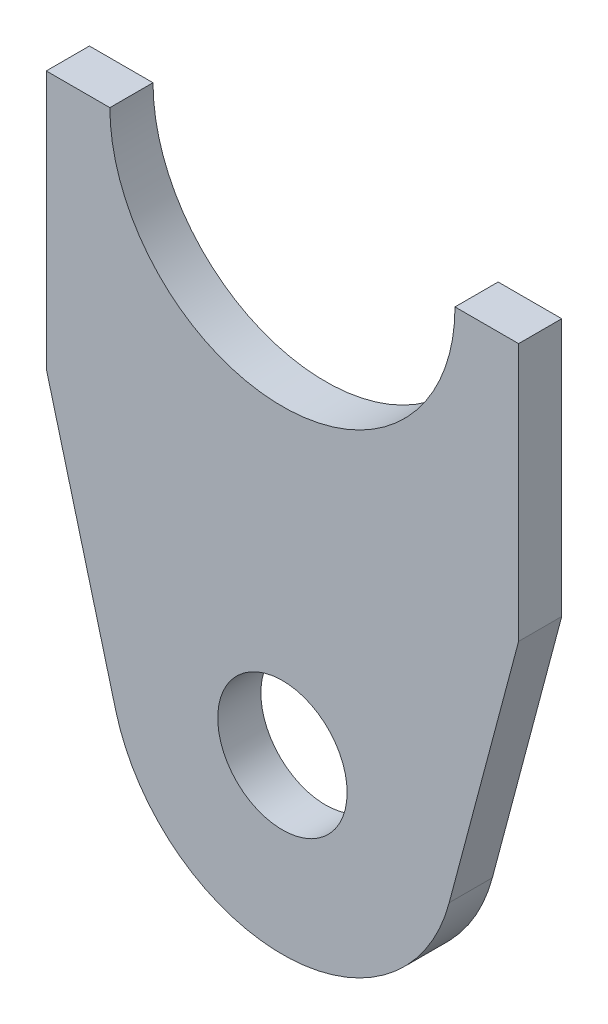
SolidWorks part; units mm, degrees
ref_plane "Front Plane" through (0, 0, 0) normal (0, 0, 1) x (1, 0, 0)
ref_plane "Top Plane" through (0, 0, 0) normal (0, 1, 0) x (1, 0, 0)
ref_plane "Right Plane" through (0, 0, 0) normal (1, 0, 0) x (0, 0, -1)
sketch "Sketch1" plane through (0, 0, 0) normal (0, 0, 1) x (1, 0, 0)
  line L0 (-17.3811, 34.925) -> (-17.3811, 15.9482)
  line L3 (-17.3811, 34.925) -> (17.3811, 34.925)
  line L5 (17.3811, 34.925) -> (17.3811, 15.9482)
  line L6 (-17.3811, 15.9482) -> (-12.2736, -3.2631)
  line L7 (17.3811, 15.9482) -> (12.2737, -3.263)
  circle A0 centre (0, 0) radius 12.7
  circle A1 centre (0, 0) radius 4.7625
  circle A2 centre (0, 34.925) radius 12.7
  dimension "D1" = 25.4
  dimension "D3" = 9.525
  dimension "D4" = 25.4
  dimension "D2" = 34.925
  dimension "D5" = 34.7622
extrude "Boss-Extrude1" add sketch "Sketch1" along normal blind 3.175
